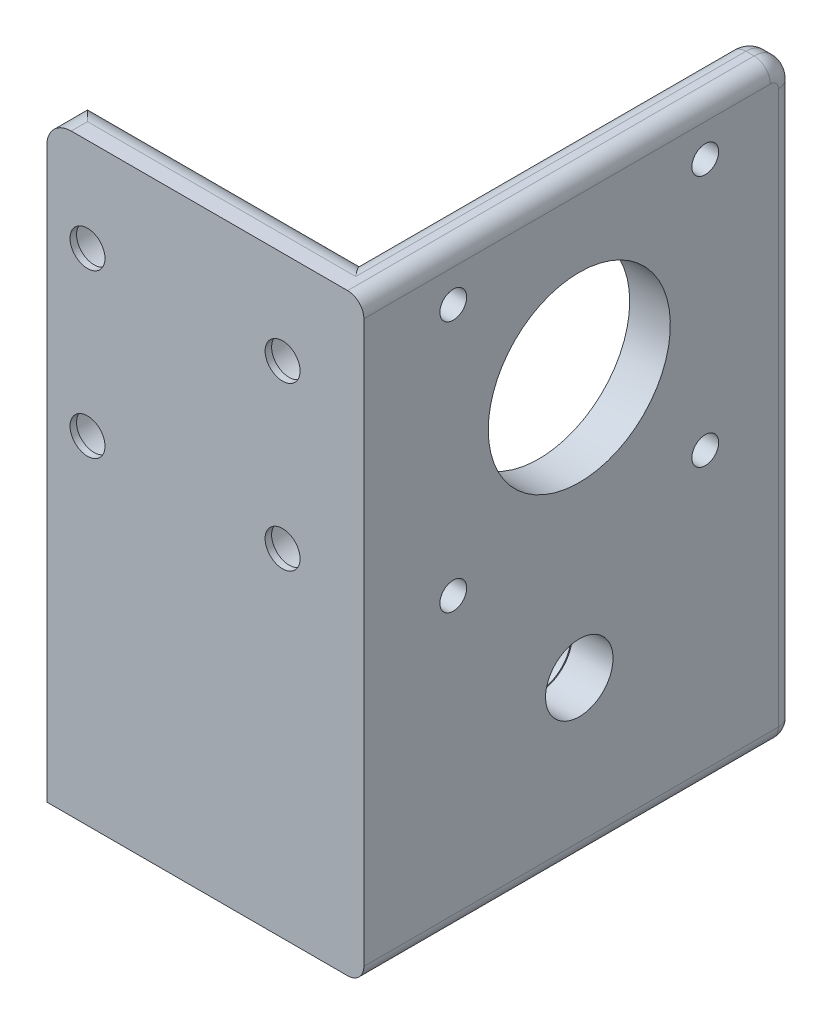
SolidWorks part; units mm, degrees
material "Balsa"
ref_plane "前视基准面" through (0, 0, 0) normal (0, 0, 1) x (1, 0, 0)
ref_plane "上视基准面" through (0, 0, 0) normal (0, 1, 0) x (1, 0, 0)
ref_plane "右视基准面" through (0, 0, 0) normal (1, 0, 0) x (0, 0, -1)
other "Configuration Table"
sketch "Sketch1" plane through (0, 0, 0) normal (0, 0, 1) x (1, 0, 0)
  line L0 (0, 21.5) -> (49.4608, 21.5) construction
  line L1 (0, 0) -> (34, 0)
  line L2 (0, 0) -> (0, 43)
  line L3 (0, 43) -> (34, 43)
  line L4 (34, 0) -> (34, 43)
  line L5 (17, 30) -> (17, -35.5313) construction
  circle A0 centre (5, 31.5) radius 2.15
  circle A1 centre (29, 31.5) radius 2.15
  circle A2 centre (5, 11.5) radius 2.15
  circle A3 centre (29, 11.5) radius 2.15
  point P17 (17, 43)
  point P18 (0, 21.5)
  dimension "D3" = 4.3
  dimension "D4" = 24
  dimension "D5" = 20
  dimension "D1" = 34
  dimension "D2" = 43
extrude "Boss-Extrude2" add sketch "Sketch1" along normal blind 5
sketch "Sketch2" plane through (0, 0, 5) normal (0, 0, 1) x (1, 0, 0)
  line L1 (0, 0) -> (34, 0) construction
  line L2 (34, 43) -> (39, 43)
  line L3 (34, 43) -> (34, 0)
  line L4 (34, 0) -> (39, 0)
  line L5 (39, 43) -> (39, 0)
  dimension "D1" = 5
extrude "Boss-Extrude3" add sketch "Sketch2" against normal blind 53
sketch "Sketch3" plane through (0, 0, 0) normal (0, 0, -1) x (-1, 0, 0)
  circle A0 centre (-5, 11.5) radius 2.15 construction
  circle A1 centre (-29, 31.5) radius 2.15 construction
  circle A2 centre (-5, 31.5) radius 2.15 construction
  circle A3 centre (-29, 11.5) radius 2.15 construction
  circle A4 centre (-5, 11.5) radius 2.15
  circle A5 centre (-29, 31.5) radius 2.15
  circle A6 centre (-5, 31.5) radius 2.15
  circle A7 centre (-29, 11.5) radius 2.15
  circle A8 centre (-29, 31.5) radius 3.55
  circle A9 centre (-5, 31.5) radius 3.55
  circle A10 centre (-5, 11.5) radius 3.55
  circle A11 centre (-29, 11.5) radius 3.55
  dimension "D1" = 7.1
  dimension "D4" = 24
  dimension "D2" = 2
  dimension "D3" = 2
extrude "Cut-Extrude1" cut sketch "Sketch3" against normal blind 4.2
sketch "Sketch5" plane through (34, 0, 0) normal (-1, 0, 0) x (0, 0, 1)
  line L0 (-43, 43) -> (-40, 43)
  line L1 (-3, 43) -> (0, 43)
  line L2 (-40, 43) -> (-3, 43)
  line L3 (-43, 0) -> (-43, 43)
  line L4 (-43, 0) -> (0, 0)
  line L5 (0, 0) -> (0, 43)
  line L6 (0, 0) -> (0, 43) construction
  line L7 (-48, 0) -> (0, 0) construction
  line L8 (-48, 43) -> (0, 43) construction
  line L9 (-48, 43) -> (-48, 0) construction
  circle A0 centre (-6, 6) radius 1.65
  circle A1 centre (-37, 6) radius 1.65
  circle A2 centre (-37, 37) radius 1.65
  circle A3 centre (-21.5, 21.5) radius 11.2
  circle A4 centre (-6, 37) radius 1.65
  dimension "D1" = 3.3
  dimension "D2" = 3.3
  dimension "D3" = 22.4
  dimension "D4" = 3.3
  dimension "D5" = 3.3
  dimension "D6" = 37
  dimension "D7" = 3
  dimension "D8" = 43
  dimension "D9" = 43
  dimension "D10" = 6
  dimension "D11" = 6
  dimension "D12" = 21.5
  dimension "D13" = 6
  dimension "D14" = 37
  dimension "D15" = 37
  dimension "D16" = 6
  dimension "D17" = 21.5
  dimension "D18" = 5
  dimension "D19" = 37
  dimension "D20" = 37
extrude "Cut-Extrude2" cut sketch "Sketch5" against normal up to surface (5 mm away) contours A2 | A3 | A4 | A0 | A1 up to face at (39, 21.5, -21.5)
fillet "Fillet1" radius 3 3 edges at (0, 43, 2.5) (36.5, 43, -48) (17, 43, 0)
sketch "Sketch7" plane through (0, 0, 0) normal (0, -1, 0) x (1, 0, 0)
  line L0 (39, -48) -> (39, 5) construction
  line L1 (0, 5) -> (39, 5)
  line L2 (0, 5) -> (0, 0)
  line L3 (0, 0) -> (34, 0)
  line L4 (39, 5) -> (39, 0)
  line L7 (39, 0) -> (39, -48)
  line L8 (39, -48) -> (34, -48)
  line L9 (34, 0) -> (34, -48)
  dimension "D1" = 5
extrude "Boss-Extrude6" add sketch "Sketch7" along normal blind 30
sketch "Sketch9" plane through (39, 0, 0) normal (1, 0, 0) x (0, 0, -1)
  line L0 (-5, -30) -> (-5, 43)
  line L1 (48.2751, -30) -> (-5, -30)
  circle A0 centre (21.5, -10.5) radius 4.15
  circle A1 centre (37, 6) radius 1.65 construction
  dimension "D1" = 8.3
  dimension "D2" = 11.2751
  dimension "D3" = 15.5
  dimension "D4" = 37
  dimension "D5" = 16.5
  dimension "D6" = 42
  dimension "D7" = 42
  dimension "D10" = 36
  dimension "D11" = 36
extrude "Cut-Extrude3" cut sketch "Sketch9" against normal blind 10 contours A0
sketch "Sketch10" plane through (34, 0, 0) normal (-1, 0, 0) x (0, 0, 1)
  line L0 (-21.5, -17.5) -> (0, -17.5)
  line L1 (0, -17.5) -> (0, -3.5)
  line L2 (0, -30) -> (0, 40) construction
  line L3 (0, -3.5) -> (-21.5, -3.5)
  line L4 (0, 40) -> (0, -30) construction
  circle A0 centre (-21.5, -10.5) radius 7
  circle M3 centre (-21.5, -10.5) radius 4.15
  line M13 (0, -30) -> (0, 40)
  dimension "D1" = 14
extrude "Boss-Extrude9" add sketch "Sketch10" along normal blind 17 contours A0 L0 L3 M13 | A0 M3 | M3
sketch "Sketch11" plane through (34, 0, 0) normal (1, 0, 0) x (0, 0, -1)
  circle A0 centre (21.5, -10.5) radius 4
  dimension "D1" = 8
extrude "Cut-Extrude4" cut sketch "Sketch11" against normal blind 5
fillet "Fillet5" radius 2 2 edges at (17, -30, 0) (36.5, -30, -48)
fillet "Fillet6" radius 2 3 edges at (25.5, -3.5, 0) (17, -10.5, 0) (25.5, -17.5, 0)
fillet "Fillet7" radius 2 10 edges at (39, -30, -20.5) (39, -29.4142, -47.4142) (39, 43, -20) (39, 42.1213, -47.1213) (34, 43, -21) (34, 42.1213, -47.1213) (34, -30, -22) (34, -29.4142, -47.4142) (39, 6, -48) (34, 6, -48)
